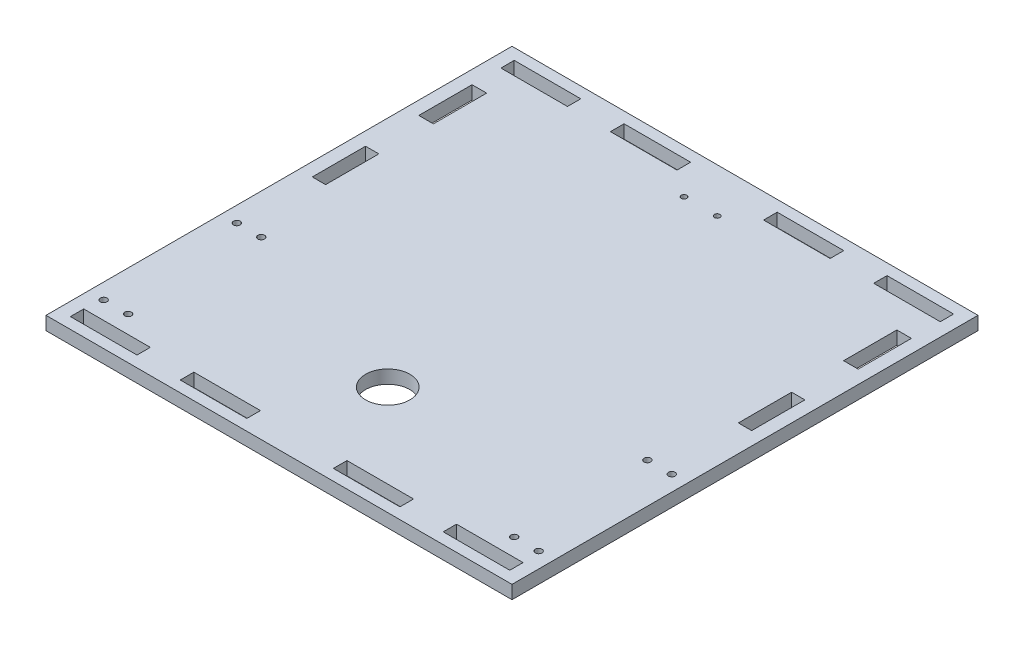
SolidWorks part; units mm, degrees
ref_plane "Front Plane" through (0, 0, 0) normal (0, 0, 1) x (1, 0, 0)
ref_plane "Top Plane" through (0, 0, 0) normal (0, 1, 0) x (1, 0, 0)
ref_plane "Right Plane" through (0, 0, 0) normal (1, 0, 0) x (0, 0, -1)
sketch "Sketch1" plane through (0, 0, 0) normal (0, 1, 0) x (1, 0, 0)
  line L0 (-0.8509, 100.6165) -> (-0.8509, -109.3835) construction
  line L5 (-105.8509, 100.6165) -> (104.1491, 100.6165)
  line L6 (-105.8509, 100.6165) -> (-105.8509, -109.3835)
  line L7 (-105.8509, -109.3835) -> (104.1491, -109.3835)
  line L8 (104.1491, 100.6165) -> (104.1491, -109.3835)
  line L9 (-105.8509, -4.3835) -> (104.1491, -4.3835) construction
  line L10 (-105.8509, -60.3835) -> (104.1491, -60.3835) construction
  line L11 (-50.3509, 95.6165) -> (-20.3509, 95.6165)
  line L12 (-99.8509, 95.6165) -> (-69.8509, 95.6165)
  line L13 (-99.8509, 95.6165) -> (-99.8509, 89.6165)
  line L14 (-99.8509, 89.6165) -> (-69.8509, 89.6165)
  line L15 (-69.8509, 95.6165) -> (-69.8509, 89.6165)
  line L16 (-50.3509, 95.6165) -> (-50.3509, 89.4824)
  line L17 (-50.3509, 89.4824) -> (-20.3509, 89.4824)
  line L18 (-20.3509, 95.6165) -> (-20.3509, 89.4824)
  line L27 (18.6491, 95.6165) -> (18.6491, 89.4824)
  line L28 (48.6491, 95.6165) -> (18.6491, 95.6165)
  line L29 (48.6491, 95.6165) -> (48.6491, 89.4824)
  line L30 (48.6491, 89.4824) -> (18.6491, 89.4824)
  line L31 (98.1491, 89.6165) -> (68.1491, 89.6165)
  line L32 (68.1491, 95.6165) -> (68.1491, 89.6165)
  line L33 (98.1491, 95.6165) -> (68.1491, 95.6165)
  line L34 (98.1491, 95.6165) -> (98.1491, 89.6165)
  line L35 (98.1491, -104.3835) -> (98.1491, -98.3835)
  line L36 (98.1491, -104.3835) -> (68.1491, -104.3835)
  line L37 (68.1491, -104.3835) -> (68.1491, -98.3835)
  line L38 (98.1491, -98.3835) -> (68.1491, -98.3835)
  line L39 (48.6491, -104.3835) -> (18.6491, -104.3835)
  line L40 (48.6491, -104.3835) -> (48.6491, -98.2494)
  line L41 (48.6491, -98.2494) -> (18.6491, -98.2494)
  line L42 (18.6491, -104.3835) -> (18.6491, -98.2494)
  line L43 (-50.3509, -104.3835) -> (-50.3509, -98.2494)
  line L44 (-50.3509, -98.2494) -> (-20.3509, -98.2494)
  line L45 (-20.3509, -104.3835) -> (-20.3509, -98.2494)
  line L46 (-50.3509, -104.3835) -> (-20.3509, -104.3835)
  line L47 (-99.8509, -98.3835) -> (-69.8509, -98.3835)
  line L48 (-69.8509, -104.3835) -> (-69.8509, -98.3835)
  line L49 (-99.8509, -104.3835) -> (-69.8509, -104.3835)
  line L50 (-99.8509, -104.3835) -> (-99.8509, -98.3835)
  line L51 (-99.8509, 76.6165) -> (-93.2787, 76.6165)
  line L52 (-99.8509, 28.6165) -> (-93.8509, 28.6165)
  line L53 (-99.8509, 28.6165) -> (-99.8509, 4.6165)
  line L54 (-99.8509, 4.6165) -> (-93.8509, 4.6165)
  line L55 (-93.8509, 28.6165) -> (-93.8509, 4.6165)
  line L56 (-99.8509, 76.6165) -> (-99.8509, 52.6165)
  line L57 (-99.8509, 52.6165) -> (-93.2787, 52.6165)
  line L58 (-93.2787, 76.6165) -> (-93.2787, 52.6165)
  line L59 (98.1491, 4.6165) -> (92.1491, 4.6165)
  line L60 (92.1491, 28.6165) -> (92.1491, 4.6165)
  line L61 (98.1491, 28.6165) -> (92.1491, 28.6165)
  line L62 (98.1491, 28.6165) -> (98.1491, 4.6165)
  line L63 (98.1491, 76.6165) -> (98.1491, 52.6165)
  line L64 (98.1491, 52.6165) -> (91.5769, 52.6165)
  line L65 (91.5769, 76.6165) -> (91.5769, 52.6165)
  line L66 (98.1491, 76.6165) -> (91.5769, 76.6165)
  circle A0 centre (-98.8509, -90.3835) radius 1.5
  circle A2 centre (-87.8509, -90.3835) radius 1.5
  circle A4 centre (-0.8509, -60.3835) radius 10
  circle A5 centre (-87.8509, -30.3835) radius 1.5
  circle A6 centre (-98.8509, -30.3835) radius 1.5
  circle A7 centre (97.1491, -90.3835) radius 1.5
  circle A8 centre (86.1491, -90.3835) radius 1.5
  circle A9 centre (86.1491, -30.3835) radius 1.5
  circle A10 centre (97.1491, -30.3835) radius 1.5
  circle A11 centre (-8.3249, 80.6165) radius 1.25
  circle A12 centre (6.6231, 80.6165) radius 1.25
  point P72 (-96.8509, 28.6165)
  dimension "D3" = 30
  dimension "D4" = 3
  dimension "D5" = 7
  dimension "D6" = 20
  dimension "D10" = 2.5
  dimension "D1" = 210
  dimension "D2" = 210
  dimension "D7" = 49
  dimension "D8" = 18
  dimension "D9" = 30
  dimension "D11" = 7.474
  dimension "D12" = 20
  dimension "D13" = 6
  dimension "D14" = 30
  dimension "D15" = 5
  dimension "D16" = 6
  dimension "D17" = 19.5
  dimension "D18" = 5
  dimension "D19" = 30
  dimension "D20" = 24
  dimension "D21" = 35
  dimension "D22" = 6
  dimension "D23" = 24
  dimension "D24" = 6
  dimension "D25" = 6
  dimension "D26" = 24
extrude "Boss-Extrude1" add sketch "Sketch1" along normal blind 6
